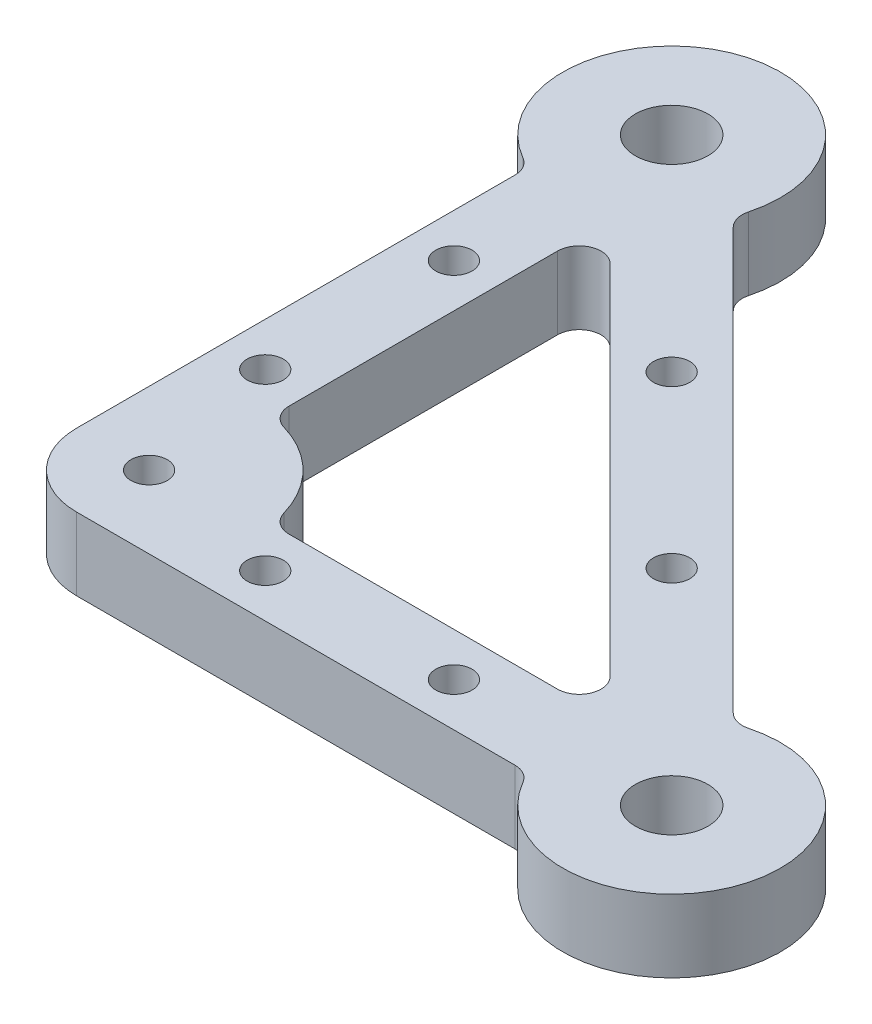
SolidWorks part; units mm, degrees
ref_plane "Front Plane" through (0, 0, 0) normal (0, 0, 1) x (1, 0, 0)
ref_plane "Top Plane" through (0, 0, 0) normal (0, 1, 0) x (1, 0, 0)
ref_plane "Right Plane" through (0, 0, 0) normal (1, 0, 0) x (0, 0, -1)
sketch "Sketch1" plane through (0, 0, 0) normal (0, 1, 0) x (1, 0, 0)
  line L0 (0, 0) -> (80, 0) construction
  line L1 (80, 0) -> (0, 80) construction
  line L2 (0, 80) -> (0, 0) construction
  line L3 (64.4115, -6) -> (4, -6)
  line L4 (-6, 64.4115) -> (-6, 4)
  line L5 (73.2199, 15.2653) -> (15.2653, 73.2199)
  line L6 (21.2916, 6) -> (58.2721, 6)
  line L11 (6, 58.2721) -> (6, 21.2916)
  line L13 (84.2426, 4.2426) -> (4.2426, 84.2426) construction
  line L14 (60.3934, 11.1213) -> (11.1213, 60.3934)
  arc A1 (14.4889, 76.1177) -> (-7.5, 67.0096) centre (0, 80) ccw
  circle A2 centre (0, 80) radius 5
  circle A3 centre (80, 0) radius 5
  arc A4 (67.0096, -7.5) -> (76.1177, 14.4889) centre (80, 0) ccw
  arc A5 (4, -6) -> (-6, 4) centre (4, 4) cw
  arc A6 (64.4115, -6) -> (67.0096, -7.5) centre (64.4115, -9) cw
  arc A7 (73.2199, 15.2653) -> (76.1177, 14.4889) centre (75.3413, 17.3867) ccw
  arc A8 (15.2653, 73.2199) -> (14.4889, 76.1177) centre (17.3867, 75.3413) cw
  arc A9 (-6, 64.4115) -> (-7.5, 67.0096) centre (-9, 64.4115) ccw
  circle A10 centre (28.2843, 51.7157) radius 2.5
  circle A11 centre (51.7157, 28.2843) radius 2.5
  circle A12 centre (4, 4) radius 2.5
  circle A13 centre (24, 0) radius 2.5
  circle A14 centre (50, 0) radius 2.5
  circle A15 centre (0, 24) radius 2.5
  circle A16 centre (0, 50) radius 2.5
  arc A18 (60.3934, 11.1213) -> (58.2721, 6) centre (58.2721, 9) cw
  arc A20 (11.1213, 60.3934) -> (6, 58.2721) centre (9, 58.2721) ccw
  arc A24 (18.4097, 8.1667) -> (8.1667, 18.4097) centre (4, 4) ccw
  arc A25 (6, 21.2916) -> (8.1667, 18.4097) centre (9, 21.2916) ccw
  arc A26 (21.2916, 6) -> (18.4097, 8.1667) centre (21.2916, 9) cw
  dimension "D1" = 30
  dimension "D2" = 10
  dimension "D5" = 10
  dimension "D6" = 10
  dimension "D7" = 3
  dimension "D8" = 5
  dimension "D10" = 5
  dimension "D11" = 5
  dimension "D13" = 5
  dimension "D14" = 5
  dimension "D15" = 5
  dimension "D16" = 5
  dimension "D27" = 15
  dimension "D28" = 6
  dimension "D30" = 15
  dimension "D31" = 3
  dimension "D32" = 3
  dimension "D3" = 80
  dimension "D4" = 80
  dimension "D17" = 40
  dimension "D18" = 40
  dimension "D19" = 26
  dimension "D20" = 30
  dimension "D21" = 20
  dimension "D22" = 26
  dimension "D23" = 30
  dimension "D24" = 4
  dimension "D25" = 12
  dimension "D26" = 6
  dimension "D29" = 12
  dimension "D12" = 12
  dimension "D33" = 9
  dimension "D9" = 6
extrude "Boss-Extrude1" add sketch "Sketch1" along normal blind 10
